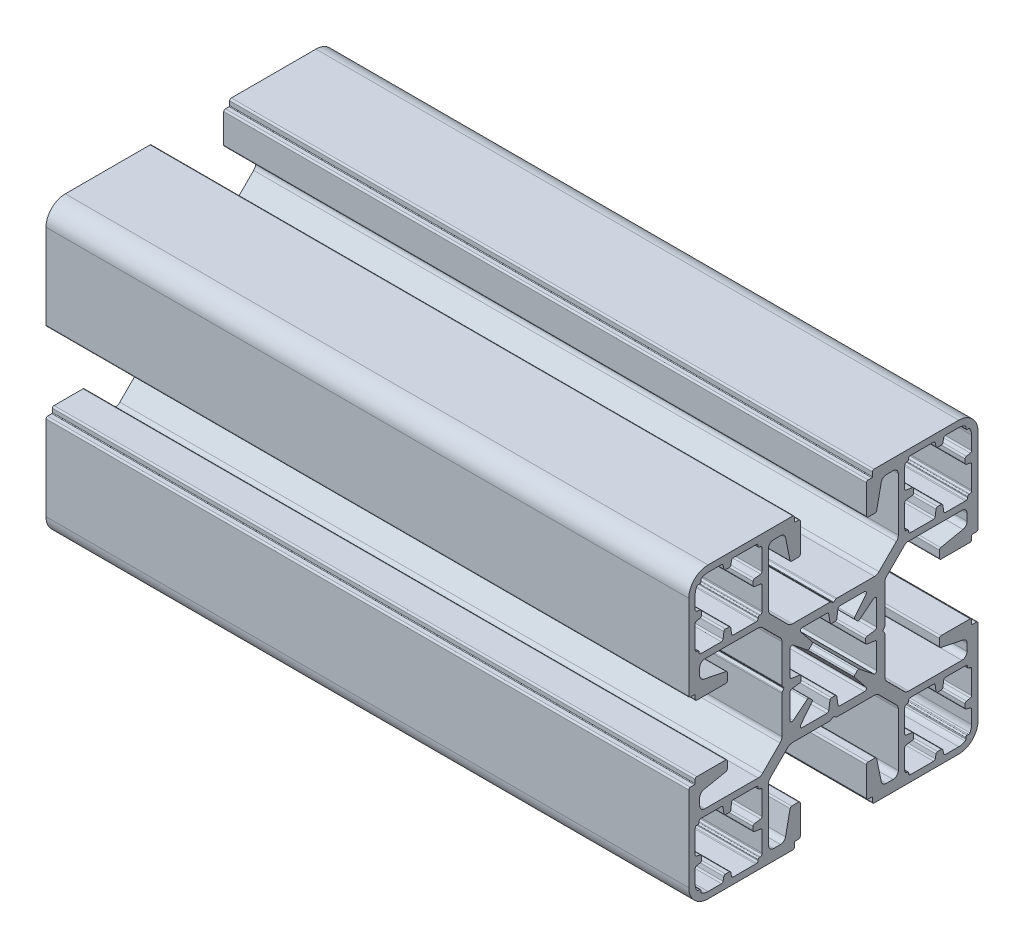
SolidWorks part; units mm, degrees
material "6063-T6"
ref_plane "Спереди" through (0, 0, 0) normal (0, 0, 1) x (1, 0, 0)
ref_plane "Сверху" through (0, 0, 0) normal (0, 1, 0) x (1, 0, 0)
ref_plane "Справа" through (0, 0, 0) normal (1, 0, 0) x (0, 0, -1)
sketch "Эскиз2" plane through (0, 0, 0) normal (1, 0, 0) x (0, 0, -1)
  point P0 (0, 0)
  line B0 (-17.405, 21.5) -> (-19.5, 21.5)
  line B1 (-20.6081, 21.0252) -> (-20.6081, 20.8081)
  line B2 (-20.8081, 20.6081) -> (-21.0252, 20.6081)
  line B3 (-21.5, 19.5) -> (-21.5, 17.405)
  line B4 (-21.299, 17.1598) -> (-20.701, 17.0402)
  line B5 (-20.5, 16.7951) -> (-20.5, 16.2049)
  line B6 (-20.701, 15.9598) -> (-21.299, 15.8402)
  line B7 (-21.5, 15.595) -> (-21.5, 12.1)
  line B8 (-21.2346, 11.699) -> (-21.101, 11.699)
  line B9 (-20.901, 11.499) -> (-20.901, 11.3654)
  line B10 (-20.5, 11.1) -> (-17.4168, 11.1)
  line B11 (-17.1693, 11.3146) -> (-17.0307, 12.2854)
  line B12 (-16.7832, 12.5) -> (-16.2168, 12.5)
  line B13 (-15.9693, 12.2854) -> (-15.8307, 11.3146)
  line B14 (-15.5832, 11.1) -> (-12.1, 11.1)
  line B15 (-11.699, 11.3654) -> (-11.699, 11.499)
  line B16 (-11.499, 11.699) -> (-11.3654, 11.699)
  line B17 (-11.1, 12.1) -> (-11.1, 15.5832)
  line B18 (-11.3146, 15.8307) -> (-12.2854, 15.9693)
  line B19 (-12.5, 16.2168) -> (-12.5, 16.7832)
  line B20 (-12.2854, 17.0307) -> (-11.3146, 17.1693)
  line B21 (-11.1, 17.4168) -> (-11.1, 20.5)
  line B22 (-11.3654, 20.901) -> (-11.499, 20.901)
  line B23 (-11.699, 21.101) -> (-11.699, 21.2346)
  line B24 (-12.1, 21.5) -> (-15.595, 21.5)
  line B25 (-15.8402, 21.299) -> (-15.9598, 20.701)
  line B26 (-16.205, 20.5) -> (-16.7951, 20.5)
  line B27 (-17.0402, 20.701) -> (-17.1598, 21.299)
  line B28 (-17.405, -21.5) -> (-19.5, -21.5)
  line B29 (-20.6081, -21.0252) -> (-20.6081, -20.8081)
  line B30 (-20.8081, -20.6081) -> (-21.0252, -20.6081)
  line B31 (-21.5, -19.5) -> (-21.5, -17.405)
  line B32 (-21.299, -17.1598) -> (-20.701, -17.0402)
  line B33 (-20.5, -16.7951) -> (-20.5, -16.2049)
  line B34 (-20.701, -15.9598) -> (-21.299, -15.8402)
  line B35 (-21.5, -15.595) -> (-21.5, -12.1)
  line B36 (-21.2346, -11.699) -> (-21.101, -11.699)
  line B37 (-20.901, -11.499) -> (-20.901, -11.3654)
  line B38 (-20.5, -11.1) -> (-17.4168, -11.1)
  line B39 (-17.1693, -11.3146) -> (-17.0307, -12.2854)
  line B40 (-16.7832, -12.5) -> (-16.2168, -12.5)
  line B41 (-15.9693, -12.2854) -> (-15.8307, -11.3146)
  line B42 (-15.5832, -11.1) -> (-12.1, -11.1)
  line B43 (-11.699, -11.3654) -> (-11.699, -11.499)
  line B44 (-11.499, -11.699) -> (-11.3654, -11.699)
  line B45 (-11.1, -12.1) -> (-11.1, -15.5832)
  line B46 (-11.3146, -15.8307) -> (-12.2854, -15.9693)
  line B47 (-12.5, -16.2168) -> (-12.5, -16.7832)
  line B48 (-12.2854, -17.0307) -> (-11.3146, -17.1693)
  line B49 (-11.1, -17.4168) -> (-11.1, -20.5)
  line B50 (-11.3654, -20.901) -> (-11.499, -20.901)
  line B51 (-11.699, -21.101) -> (-11.699, -21.2346)
  line B52 (-12.1, -21.5) -> (-15.595, -21.5)
  line B53 (-15.8402, -21.299) -> (-15.9598, -20.701)
  line B54 (-16.205, -20.5) -> (-16.7951, -20.5)
  line B55 (-17.0402, -20.701) -> (-17.1598, -21.299)
  line B56 (17.405, 21.5) -> (19.5, 21.5)
  line B57 (20.6081, 21.0252) -> (20.6081, 20.8081)
  line B58 (20.8081, 20.6081) -> (21.0252, 20.6081)
  line B59 (21.5, 19.5) -> (21.5, 17.405)
  line B60 (21.299, 17.1598) -> (20.701, 17.0402)
  line B61 (20.5, 16.795) -> (20.5, 16.2049)
  line B62 (20.701, 15.9598) -> (21.299, 15.8402)
  line B63 (21.5, 15.595) -> (21.5, 12.1)
  line B64 (21.2346, 11.699) -> (21.101, 11.699)
  line B65 (20.901, 11.499) -> (20.901, 11.3654)
  line B66 (20.5, 11.1) -> (17.4168, 11.1)
  line B67 (17.1693, 11.3146) -> (17.0307, 12.2854)
  line B68 (16.7832, 12.5) -> (16.2168, 12.5)
  line B69 (15.9693, 12.2854) -> (15.8307, 11.3146)
  line B70 (15.5832, 11.1) -> (12.1, 11.1)
  line B71 (11.699, 11.3654) -> (11.699, 11.499)
  line B72 (11.499, 11.699) -> (11.3654, 11.699)
  line B73 (11.1, 12.1) -> (11.1, 15.5832)
  line B74 (11.3146, 15.8307) -> (12.2854, 15.9693)
  line B75 (12.5, 16.2168) -> (12.5, 16.7832)
  line B76 (12.2854, 17.0307) -> (11.3146, 17.1693)
  line B77 (11.1, 17.4168) -> (11.1, 20.5)
  line B78 (11.3654, 20.901) -> (11.499, 20.901)
  line B79 (11.699, 21.101) -> (11.699, 21.2346)
  line B80 (12.1, 21.5) -> (15.595, 21.5)
  line B81 (15.8402, 21.299) -> (15.9598, 20.701)
  line B82 (16.2049, 20.5) -> (16.795, 20.5)
  line B83 (17.0402, 20.701) -> (17.1598, 21.299)
  line B84 (17.405, -21.5) -> (19.5, -21.5)
  line B85 (20.6081, -21.0252) -> (20.6081, -20.8081)
  line B86 (20.8081, -20.6081) -> (21.0252, -20.6081)
  line B87 (21.5, -19.5) -> (21.5, -17.405)
  line B88 (21.299, -17.1598) -> (20.701, -17.0402)
  line B89 (20.5, -16.795) -> (20.5, -16.2049)
  line B90 (20.701, -15.9598) -> (21.299, -15.8402)
  line B91 (21.5, -15.595) -> (21.5, -12.1)
  line B92 (21.2346, -11.699) -> (21.101, -11.699)
  line B93 (20.901, -11.499) -> (20.901, -11.3654)
  line B94 (20.5, -11.1) -> (17.4168, -11.1)
  line B95 (17.1693, -11.3146) -> (17.0307, -12.2854)
  line B96 (16.7832, -12.5) -> (16.2168, -12.5)
  line B97 (15.9693, -12.2854) -> (15.8307, -11.3146)
  line B98 (15.5832, -11.1) -> (12.1, -11.1)
  line B99 (11.699, -11.3654) -> (11.699, -11.499)
  line B100 (11.499, -11.699) -> (11.3654, -11.699)
  line B101 (11.1, -12.1) -> (11.1, -15.5832)
  line B102 (11.3146, -15.8307) -> (12.2854, -15.9693)
  line B103 (12.5, -16.2168) -> (12.5, -16.7832)
  line B104 (12.2854, -17.0307) -> (11.3146, -17.1693)
  line B105 (11.1, -17.4168) -> (11.1, -20.5)
  line B106 (11.3654, -20.901) -> (11.499, -20.901)
  line B107 (11.699, -21.101) -> (11.699, -21.2346)
  line B108 (12.1, -21.5) -> (15.595, -21.5)
  line B109 (15.8402, -21.299) -> (15.9598, -20.701)
  line B110 (16.2049, -20.5) -> (16.795, -20.5)
  line B111 (17.0402, -20.701) -> (17.1598, -21.299)
  line B112 (-6.325, -22.5) -> (-19.5, -22.5)
  line B113 (-22.5, -19.5) -> (-22.5, -6.325)
  line B114 (-22.25, -6.075) -> (-21.6, -6.075)
  line B115 (-21.5, -5.975) -> (-21.5, -5.4)
  line B116 (-21.25, -5.15) -> (-16.75, -5.15)
  line B117 (-16.5, -5.4) -> (-16.5, -6.4957)
  line B118 (-16.7001, -6.7407) -> (-20.1595, -7.4447)
  line B119 (-20.8, -8.2286) -> (-20.8, -9.3)
  line B120 (-20, -10.1) -> (-11.7163, -10.1)
  line B121 (-11.0092, -9.8071) -> (-8.2929, -7.0908)
  line B122 (-8, -6.3837) -> (-8, -0.5305)
  line B123 (-7.9531, -0.3846) -> (-7.7188, -0.0583)
  line B124 (-7.7188, 0.0583) -> (-7.9531, 0.3846)
  line B125 (-8, 0.5305) -> (-8, 6.3837)
  line B126 (-8.2929, 7.0908) -> (-11.0092, 9.8071)
  line B127 (-11.7163, 10.1) -> (-20, 10.1)
  line B128 (-20.8, 9.3) -> (-20.8, 8.2286)
  line B129 (-20.1595, 7.4447) -> (-16.7001, 6.7407)
  line B130 (-16.5, 6.4957) -> (-16.5, 5.4)
  line B131 (-16.75, 5.15) -> (-21.25, 5.15)
  line B132 (-21.5, 5.4) -> (-21.5, 5.975)
  line B133 (-21.6, 6.075) -> (-22.25, 6.075)
  line B134 (-22.5, 6.325) -> (-22.5, 19.5)
  line B135 (-19.5, 22.5) -> (-6.325, 22.5)
  line B136 (-6.075, 22.25) -> (-6.075, 21.6)
  line B137 (-5.975, 21.5) -> (-5.4, 21.5)
  line B138 (-5.15, 21.25) -> (-5.15, 16.75)
  line B139 (-5.4, 16.5) -> (-6.4957, 16.5)
  line B140 (-6.7407, 16.7001) -> (-7.4447, 20.1595)
  line B141 (-8.2286, 20.8) -> (-9.3, 20.8)
  line B142 (-10.1, 20) -> (-10.1, 11.7163)
  line B143 (-9.8071, 11.0092) -> (-7.0908, 8.2929)
  line B144 (-6.3837, 8) -> (-0.5305, 8)
  line B145 (-0.3846, 7.9531) -> (-0.0583, 7.7188)
  line B146 (0.0583, 7.7188) -> (0.3846, 7.9531)
  line B147 (0.5305, 8) -> (6.3837, 8)
  line B148 (7.0908, 8.2929) -> (9.8071, 11.0092)
  line B149 (10.1, 11.7163) -> (10.1, 20)
  line B150 (9.3, 20.8) -> (8.2286, 20.8)
  line B151 (7.4447, 20.1595) -> (6.7407, 16.7001)
  line B152 (6.4957, 16.5) -> (5.4, 16.5)
  line B153 (5.15, 16.75) -> (5.15, 21.25)
  line B154 (5.4, 21.5) -> (5.975, 21.5)
  line B155 (6.075, 21.6) -> (6.075, 22.25)
  line B156 (6.325, 22.5) -> (19.5, 22.5)
  line B157 (22.5, 19.5) -> (22.5, 6.325)
  line B158 (22.25, 6.075) -> (21.6, 6.075)
  line B159 (21.5, 5.975) -> (21.5, 5.4)
  line B160 (21.25, 5.15) -> (16.75, 5.15)
  line B161 (16.5, 5.4) -> (16.5, 6.4957)
  line B162 (16.7001, 6.7407) -> (20.1595, 7.4447)
  line B163 (20.8, 8.2286) -> (20.8, 9.3)
  line B164 (20, 10.1) -> (11.7163, 10.1)
  line B165 (11.0092, 9.8071) -> (8.2929, 7.0908)
  line B166 (8, 6.3837) -> (8, 0.5305)
  line B167 (7.9531, 0.3846) -> (7.7188, 0.0583)
  line B168 (7.7188, -0.0583) -> (7.9531, -0.3846)
  line B169 (8, -0.5305) -> (8, -6.3837)
  line B170 (8.2929, -7.0908) -> (11.0092, -9.8071)
  line B171 (11.7163, -10.1) -> (20, -10.1)
  line B172 (20.8, -9.3) -> (20.8, -8.2286)
  line B173 (20.1595, -7.4447) -> (16.7001, -6.7407)
  line B174 (16.5, -6.4957) -> (16.5, -5.4)
  line B175 (16.75, -5.15) -> (21.25, -5.15)
  line B176 (21.5, -5.4) -> (21.5, -5.975)
  line B177 (21.6, -6.075) -> (22.25, -6.075)
  line B178 (22.5, -6.325) -> (22.5, -19.5)
  line B179 (19.5, -22.5) -> (6.325, -22.5)
  line B180 (6.075, -22.25) -> (6.075, -21.6)
  line B181 (5.975, -21.5) -> (5.4, -21.5)
  line B182 (5.15, -21.25) -> (5.15, -16.75)
  line B183 (5.4, -16.5) -> (6.4957, -16.5)
  line B184 (6.7407, -16.7001) -> (7.4447, -20.1595)
  line B185 (8.2286, -20.8) -> (9.3, -20.8)
  line B186 (10.1, -20) -> (10.1, -11.7163)
  line B187 (9.8071, -11.0092) -> (7.0908, -8.2929)
  line B188 (6.3837, -8) -> (0.5305, -8)
  line B189 (0.3846, -7.9531) -> (0.0583, -7.7188)
  line B190 (-0.0583, -7.7188) -> (-0.3846, -7.9531)
  line B191 (-0.5305, -8) -> (-6.3837, -8)
  line B192 (-7.0908, -8.2929) -> (-9.8071, -11.0092)
  line B193 (-10.1, -11.7163) -> (-10.1, -20)
  line B194 (-9.3, -20.8) -> (-8.2286, -20.8)
  line B195 (-7.4447, -20.1595) -> (-6.7407, -16.7001)
  line B196 (-6.4957, -16.5) -> (-5.4, -16.5)
  line B197 (-5.15, -16.75) -> (-5.15, -21.25)
  line B198 (-5.4, -21.5) -> (-5.975, -21.5)
  line B199 (-6.075, -21.6) -> (-6.075, -22.25)
  line B200 (-4.8423, -6.74) -> (-1.01, -6.74)
  line B201 (-0.713, -6.4827) -> (-0.5308, -5.2144)
  line B202 (-0.2834, -5) -> (0.2834, -5)
  line B203 (0.5308, -5.2144) -> (0.713, -6.4827)
  line B204 (1.01, -6.74) -> (4.8423, -6.74)
  line B205 (5.0763, -6.2524) -> (3.3221, -4.0638)
  line B206 (3.3404, -3.7307) -> (3.7307, -3.3404)
  line B207 (4.0638, -3.3221) -> (6.2524, -5.0763)
  line B208 (6.74, -4.8423) -> (6.74, -1.01)
  line B209 (6.4827, -0.713) -> (5.2144, -0.5308)
  line B210 (5, -0.2834) -> (5, 0.2834)
  line B211 (5.2144, 0.5308) -> (6.4827, 0.713)
  line B212 (6.74, 1.01) -> (6.74, 4.8423)
  line B213 (6.2524, 5.0763) -> (4.0638, 3.3221)
  line B214 (3.7307, 3.3404) -> (3.3404, 3.7307)
  line B215 (3.3221, 4.0638) -> (5.0763, 6.2524)
  line B216 (4.8423, 6.74) -> (1.01, 6.74)
  line B217 (0.713, 6.4827) -> (0.5308, 5.2144)
  line B218 (0.2834, 5) -> (-0.2834, 5)
  line B219 (-0.5308, 5.2144) -> (-0.713, 6.4827)
  line B220 (-1.01, 6.74) -> (-4.8423, 6.74)
  line B221 (-5.0763, 6.2524) -> (-3.3221, 4.0638)
  line B222 (-3.3404, 3.7307) -> (-3.7307, 3.3404)
  line B223 (-4.0639, 3.3221) -> (-6.2524, 5.0763)
  line B224 (-6.74, 4.8423) -> (-6.74, 1.01)
  line B225 (-6.4827, 0.713) -> (-5.2144, 0.5308)
  line B226 (-5, 0.2834) -> (-5, -0.2834)
  line B227 (-5.2144, -0.5308) -> (-6.4827, -0.713)
  line B228 (-6.74, -1.01) -> (-6.74, -4.8423)
  line B229 (-6.2524, -5.0763) -> (-4.0639, -3.3221)
  line B230 (-3.7307, -3.3404) -> (-3.3404, -3.7307)
  line B231 (-3.3221, -4.0638) -> (-5.0763, -6.2524)
  arc B232 (-19.5, 21.5) -> (-20.4807, 21.243) centre (-19.5, 19.5) ccw
  arc B233 (-20.4807, 21.243) -> (-20.6081, 21.0252) centre (-20.3581, 21.0252) ccw
  arc B234 (-20.8081, 20.6081) -> (-20.6081, 20.8081) centre (-20.8081, 20.8081) ccw
  arc B235 (-21.0252, 20.6081) -> (-21.243, 20.4807) centre (-21.0252, 20.3581) ccw
  arc B236 (-21.243, 20.4807) -> (-21.5, 19.5) centre (-19.5, 19.5) ccw
  arc B237 (-21.5, 17.405) -> (-21.299, 17.1598) centre (-21.25, 17.405) ccw
  arc B238 (-20.5, 16.7951) -> (-20.701, 17.0402) centre (-20.75, 16.7951) ccw
  arc B239 (-20.701, 15.9598) -> (-20.5, 16.2049) centre (-20.75, 16.2049) ccw
  arc B240 (-21.299, 15.8402) -> (-21.5, 15.595) centre (-21.25, 15.595) ccw
  arc B241 (-21.5, 12.1) -> (-21.4795, 11.8986) centre (-20.5, 12.1) ccw
  arc B242 (-21.4795, 11.8986) -> (-21.2346, 11.699) centre (-21.2346, 11.949) ccw
  arc B243 (-20.901, 11.499) -> (-21.101, 11.699) centre (-21.101, 11.499) ccw
  arc B244 (-20.901, 11.3654) -> (-20.7014, 11.1205) centre (-20.651, 11.3654) ccw
  arc B245 (-20.7014, 11.1205) -> (-20.5, 11.1) centre (-20.5, 12.1) ccw
  arc B246 (-17.4168, 11.1) -> (-17.1693, 11.3146) centre (-17.4168, 11.35) ccw
  arc B247 (-16.7832, 12.5) -> (-17.0307, 12.2854) centre (-16.7832, 12.25) ccw
  arc B248 (-15.9693, 12.2854) -> (-16.2168, 12.5) centre (-16.2168, 12.25) ccw
  arc B249 (-15.8307, 11.3146) -> (-15.5832, 11.1) centre (-15.5832, 11.35) ccw
  arc B250 (-12.1, 11.1) -> (-11.8986, 11.1205) centre (-12.1, 12.1) ccw
  arc B251 (-11.8986, 11.1205) -> (-11.699, 11.3654) centre (-11.949, 11.3654) ccw
  arc B252 (-11.499, 11.699) -> (-11.699, 11.499) centre (-11.499, 11.499) ccw
  arc B253 (-11.3654, 11.699) -> (-11.1205, 11.8986) centre (-11.3654, 11.949) ccw
  arc B254 (-11.1205, 11.8986) -> (-11.1, 12.1) centre (-12.1, 12.1) ccw
  arc B255 (-11.1, 15.5832) -> (-11.3146, 15.8307) centre (-11.35, 15.5832) ccw
  arc B256 (-12.5, 16.2168) -> (-12.2854, 15.9693) centre (-12.25, 16.2168) ccw
  arc B257 (-12.2854, 17.0307) -> (-12.5, 16.7832) centre (-12.25, 16.7832) ccw
  arc B258 (-11.3146, 17.1693) -> (-11.1, 17.4168) centre (-11.35, 17.4168) ccw
  arc B259 (-11.1, 20.5) -> (-11.1205, 20.7014) centre (-12.1, 20.5) ccw
  arc B260 (-11.1205, 20.7014) -> (-11.3654, 20.901) centre (-11.3654, 20.651) ccw
  arc B261 (-11.699, 21.101) -> (-11.499, 20.901) centre (-11.499, 21.101) ccw
  arc B262 (-11.699, 21.2346) -> (-11.8986, 21.4795) centre (-11.949, 21.2346) ccw
  arc B263 (-11.8986, 21.4795) -> (-12.1, 21.5) centre (-12.1, 20.5) ccw
  arc B264 (-15.595, 21.5) -> (-15.8402, 21.299) centre (-15.595, 21.25) ccw
  arc B265 (-16.205, 20.5) -> (-15.9598, 20.701) centre (-16.205, 20.75) ccw
  arc B266 (-17.0402, 20.701) -> (-16.7951, 20.5) centre (-16.7951, 20.75) ccw
  arc B267 (-17.1598, 21.299) -> (-17.405, 21.5) centre (-17.405, 21.25) ccw
  arc B268 (-20.4807, -21.243) -> (-19.5, -21.5) centre (-19.5, -19.5) ccw
  arc B269 (-20.6081, -21.0252) -> (-20.4807, -21.243) centre (-20.3581, -21.0252) ccw
  arc B270 (-20.6081, -20.8081) -> (-20.8081, -20.6081) centre (-20.8081, -20.8081) ccw
  arc B271 (-21.243, -20.4807) -> (-21.0252, -20.6081) centre (-21.0252, -20.3581) ccw
  arc B272 (-21.5, -19.5) -> (-21.243, -20.4807) centre (-19.5, -19.5) ccw
  arc B273 (-21.299, -17.1598) -> (-21.5, -17.405) centre (-21.25, -17.405) ccw
  arc B274 (-20.701, -17.0402) -> (-20.5, -16.7951) centre (-20.75, -16.7951) ccw
  arc B275 (-20.5, -16.2049) -> (-20.701, -15.9598) centre (-20.75, -16.2049) ccw
  arc B276 (-21.5, -15.595) -> (-21.299, -15.8402) centre (-21.25, -15.595) ccw
  arc B277 (-21.4795, -11.8986) -> (-21.5, -12.1) centre (-20.5, -12.1) ccw
  arc B278 (-21.2346, -11.699) -> (-21.4795, -11.8986) centre (-21.2346, -11.949) ccw
  arc B279 (-21.101, -11.699) -> (-20.901, -11.499) centre (-21.101, -11.499) ccw
  arc B280 (-20.7014, -11.1205) -> (-20.901, -11.3654) centre (-20.651, -11.3654) ccw
  arc B281 (-20.5, -11.1) -> (-20.7014, -11.1205) centre (-20.5, -12.1) ccw
  arc B282 (-17.1693, -11.3146) -> (-17.4168, -11.1) centre (-17.4168, -11.35) ccw
  arc B283 (-17.0307, -12.2854) -> (-16.7832, -12.5) centre (-16.7832, -12.25) ccw
  arc B284 (-16.2168, -12.5) -> (-15.9693, -12.2854) centre (-16.2168, -12.25) ccw
  arc B285 (-15.5832, -11.1) -> (-15.8307, -11.3146) centre (-15.5832, -11.35) ccw
  arc B286 (-11.8986, -11.1205) -> (-12.1, -11.1) centre (-12.1, -12.1) ccw
  arc B287 (-11.699, -11.3654) -> (-11.8986, -11.1205) centre (-11.949, -11.3654) ccw
  arc B288 (-11.699, -11.499) -> (-11.499, -11.699) centre (-11.499, -11.499) ccw
  arc B289 (-11.1205, -11.8986) -> (-11.3654, -11.699) centre (-11.3654, -11.949) ccw
  arc B290 (-11.1, -12.1) -> (-11.1205, -11.8986) centre (-12.1, -12.1) ccw
  arc B291 (-11.3146, -15.8307) -> (-11.1, -15.5832) centre (-11.35, -15.5832) ccw
  arc B292 (-12.2854, -15.9693) -> (-12.5, -16.2168) centre (-12.25, -16.2168) ccw
  arc B293 (-12.5, -16.7832) -> (-12.2854, -17.0307) centre (-12.25, -16.7832) ccw
  arc B294 (-11.1, -17.4168) -> (-11.3146, -17.1693) centre (-11.35, -17.4168) ccw
  arc B295 (-11.1205, -20.7014) -> (-11.1, -20.5) centre (-12.1, -20.5) ccw
  arc B296 (-11.3654, -20.901) -> (-11.1205, -20.7014) centre (-11.3654, -20.651) ccw
  arc B297 (-11.499, -20.901) -> (-11.699, -21.101) centre (-11.499, -21.101) ccw
  arc B298 (-11.8986, -21.4795) -> (-11.699, -21.2346) centre (-11.949, -21.2346) ccw
  arc B299 (-12.1, -21.5) -> (-11.8986, -21.4795) centre (-12.1, -20.5) ccw
  arc B300 (-15.8402, -21.299) -> (-15.595, -21.5) centre (-15.595, -21.25) ccw
  arc B301 (-15.9598, -20.701) -> (-16.205, -20.5) centre (-16.205, -20.75) ccw
  arc B302 (-16.7951, -20.5) -> (-17.0402, -20.701) centre (-16.7951, -20.75) ccw
  arc B303 (-17.405, -21.5) -> (-17.1598, -21.299) centre (-17.405, -21.25) ccw
  arc B304 (20.4807, 21.243) -> (19.5, 21.5) centre (19.5, 19.5) ccw
  arc B305 (20.6081, 21.0252) -> (20.4807, 21.243) centre (20.3581, 21.0252) ccw
  arc B306 (20.6081, 20.8081) -> (20.8081, 20.6081) centre (20.8081, 20.8081) ccw
  arc B307 (21.243, 20.4807) -> (21.0252, 20.6081) centre (21.0252, 20.3581) ccw
  arc B308 (21.5, 19.5) -> (21.243, 20.4807) centre (19.5, 19.5) ccw
  arc B309 (21.299, 17.1598) -> (21.5, 17.405) centre (21.25, 17.405) ccw
  arc B310 (20.701, 17.0402) -> (20.5, 16.795) centre (20.75, 16.795) ccw
  arc B311 (20.5, 16.2049) -> (20.701, 15.9598) centre (20.75, 16.2049) ccw
  arc B312 (21.5, 15.595) -> (21.299, 15.8402) centre (21.25, 15.595) ccw
  arc B313 (21.4795, 11.8986) -> (21.5, 12.1) centre (20.5, 12.1) ccw
  arc B314 (21.2346, 11.699) -> (21.4795, 11.8986) centre (21.2346, 11.949) ccw
  arc B315 (21.101, 11.699) -> (20.901, 11.499) centre (21.101, 11.499) ccw
  arc B316 (20.7014, 11.1205) -> (20.901, 11.3654) centre (20.651, 11.3654) ccw
  arc B317 (20.5, 11.1) -> (20.7014, 11.1205) centre (20.5, 12.1) ccw
  arc B318 (17.1693, 11.3146) -> (17.4168, 11.1) centre (17.4168, 11.35) ccw
  arc B319 (17.0307, 12.2854) -> (16.7832, 12.5) centre (16.7832, 12.25) ccw
  arc B320 (16.2168, 12.5) -> (15.9693, 12.2854) centre (16.2168, 12.25) ccw
  arc B321 (15.5832, 11.1) -> (15.8307, 11.3146) centre (15.5832, 11.35) ccw
  arc B322 (11.8986, 11.1205) -> (12.1, 11.1) centre (12.1, 12.1) ccw
  arc B323 (11.699, 11.3654) -> (11.8986, 11.1205) centre (11.949, 11.3654) ccw
  arc B324 (11.699, 11.499) -> (11.499, 11.699) centre (11.499, 11.499) ccw
  arc B325 (11.1205, 11.8986) -> (11.3654, 11.699) centre (11.3654, 11.949) ccw
  arc B326 (11.1, 12.1) -> (11.1205, 11.8986) centre (12.1, 12.1) ccw
  arc B327 (11.3146, 15.8307) -> (11.1, 15.5832) centre (11.35, 15.5832) ccw
  arc B328 (12.2854, 15.9693) -> (12.5, 16.2168) centre (12.25, 16.2168) ccw
  arc B329 (12.5, 16.7832) -> (12.2854, 17.0307) centre (12.25, 16.7832) ccw
  arc B330 (11.1, 17.4168) -> (11.3146, 17.1693) centre (11.35, 17.4168) ccw
  arc B331 (11.1205, 20.7014) -> (11.1, 20.5) centre (12.1, 20.5) ccw
  arc B332 (11.3654, 20.901) -> (11.1205, 20.7014) centre (11.3654, 20.651) ccw
  arc B333 (11.499, 20.901) -> (11.699, 21.101) centre (11.499, 21.101) ccw
  arc B334 (11.8986, 21.4795) -> (11.699, 21.2346) centre (11.949, 21.2346) ccw
  arc B335 (12.1, 21.5) -> (11.8986, 21.4795) centre (12.1, 20.5) ccw
  arc B336 (15.8402, 21.299) -> (15.595, 21.5) centre (15.595, 21.25) ccw
  arc B337 (15.9598, 20.701) -> (16.2049, 20.5) centre (16.2049, 20.75) ccw
  arc B338 (16.795, 20.5) -> (17.0402, 20.701) centre (16.795, 20.75) ccw
  arc B339 (17.405, 21.5) -> (17.1598, 21.299) centre (17.405, 21.25) ccw
  arc B340 (19.5, -21.5) -> (20.4807, -21.243) centre (19.5, -19.5) ccw
  arc B341 (20.4807, -21.243) -> (20.6081, -21.0252) centre (20.3581, -21.0252) ccw
  arc B342 (20.8081, -20.6081) -> (20.6081, -20.8081) centre (20.8081, -20.8081) ccw
  arc B343 (21.0252, -20.6081) -> (21.243, -20.4807) centre (21.0252, -20.3581) ccw
  arc B344 (21.243, -20.4807) -> (21.5, -19.5) centre (19.5, -19.5) ccw
  arc B345 (21.5, -17.405) -> (21.299, -17.1598) centre (21.25, -17.405) ccw
  arc B346 (20.5, -16.795) -> (20.701, -17.0402) centre (20.75, -16.795) ccw
  arc B347 (20.701, -15.9598) -> (20.5, -16.2049) centre (20.75, -16.2049) ccw
  arc B348 (21.299, -15.8402) -> (21.5, -15.595) centre (21.25, -15.595) ccw
  arc B349 (21.5, -12.1) -> (21.4795, -11.8986) centre (20.5, -12.1) ccw
  arc B350 (21.4795, -11.8986) -> (21.2346, -11.699) centre (21.2346, -11.949) ccw
  arc B351 (20.901, -11.499) -> (21.101, -11.699) centre (21.101, -11.499) ccw
  arc B352 (20.901, -11.3654) -> (20.7014, -11.1205) centre (20.651, -11.3654) ccw
  arc B353 (20.7014, -11.1205) -> (20.5, -11.1) centre (20.5, -12.1) ccw
  arc B354 (17.4168, -11.1) -> (17.1693, -11.3146) centre (17.4168, -11.35) ccw
  arc B355 (16.7832, -12.5) -> (17.0307, -12.2854) centre (16.7832, -12.25) ccw
  arc B356 (15.9693, -12.2854) -> (16.2168, -12.5) centre (16.2168, -12.25) ccw
  arc B357 (15.8307, -11.3146) -> (15.5832, -11.1) centre (15.5832, -11.35) ccw
  arc B358 (12.1, -11.1) -> (11.8986, -11.1205) centre (12.1, -12.1) ccw
  arc B359 (11.8986, -11.1205) -> (11.699, -11.3654) centre (11.949, -11.3654) ccw
  arc B360 (11.499, -11.699) -> (11.699, -11.499) centre (11.499, -11.499) ccw
  arc B361 (11.3654, -11.699) -> (11.1205, -11.8986) centre (11.3654, -11.949) ccw
  arc B362 (11.1205, -11.8986) -> (11.1, -12.1) centre (12.1, -12.1) ccw
  arc B363 (11.1, -15.5832) -> (11.3146, -15.8307) centre (11.35, -15.5832) ccw
  arc B364 (12.5, -16.2168) -> (12.2854, -15.9693) centre (12.25, -16.2168) ccw
  arc B365 (12.2854, -17.0307) -> (12.5, -16.7832) centre (12.25, -16.7832) ccw
  arc B366 (11.3146, -17.1693) -> (11.1, -17.4168) centre (11.35, -17.4168) ccw
  arc B367 (11.1, -20.5) -> (11.1205, -20.7014) centre (12.1, -20.5) ccw
  arc B368 (11.1205, -20.7014) -> (11.3654, -20.901) centre (11.3654, -20.651) ccw
  arc B369 (11.699, -21.101) -> (11.499, -20.901) centre (11.499, -21.101) ccw
  arc B370 (11.699, -21.2346) -> (11.8986, -21.4795) centre (11.949, -21.2346) ccw
  arc B371 (11.8986, -21.4795) -> (12.1, -21.5) centre (12.1, -20.5) ccw
  arc B372 (15.595, -21.5) -> (15.8402, -21.299) centre (15.595, -21.25) ccw
  arc B373 (16.2049, -20.5) -> (15.9598, -20.701) centre (16.2049, -20.75) ccw
  arc B374 (17.0402, -20.701) -> (16.795, -20.5) centre (16.795, -20.75) ccw
  arc B375 (17.1598, -21.299) -> (17.405, -21.5) centre (17.405, -21.25) ccw
  arc B376 (-22.5, -19.5) -> (-19.5, -22.5) centre (-19.5, -19.5) ccw
  arc B377 (-22.25, -6.075) -> (-22.5, -6.325) centre (-22.25, -6.325) ccw
  arc B378 (-21.6, -6.075) -> (-21.5, -5.975) centre (-21.6, -5.975) ccw
  arc B379 (-21.25, -5.15) -> (-21.5, -5.4) centre (-21.25, -5.4) ccw
  arc B380 (-16.5, -5.4) -> (-16.75, -5.15) centre (-16.75, -5.4) ccw
  arc B381 (-16.7001, -6.7407) -> (-16.5, -6.4957) centre (-16.75, -6.4957) ccw
  arc B382 (-20.1595, -7.4447) -> (-20.8, -8.2286) centre (-20, -8.2286) ccw
  arc B383 (-20.8, -9.3) -> (-20, -10.1) centre (-20, -9.3) ccw
  arc B384 (-11.7163, -10.1) -> (-11.0092, -9.8071) centre (-11.7163, -9.1) ccw
  arc B385 (-8.2929, -7.0908) -> (-8, -6.3837) centre (-9, -6.3837) ccw
  arc B386 (-7.9531, -0.3846) -> (-8, -0.5305) centre (-7.75, -0.5305) ccw
  arc B387 (-7.7188, -0.0583) -> (-7.7188, 0.0583) centre (-7.8, 0) ccw
  arc B388 (-8, 0.5305) -> (-7.9531, 0.3846) centre (-7.75, 0.5305) ccw
  arc B389 (-8, 6.3837) -> (-8.2929, 7.0908) centre (-9, 6.3837) ccw
  arc B390 (-11.0092, 9.8071) -> (-11.7163, 10.1) centre (-11.7163, 9.1) ccw
  arc B391 (-20, 10.1) -> (-20.8, 9.3) centre (-20, 9.3) ccw
  arc B392 (-20.8, 8.2286) -> (-20.1595, 7.4447) centre (-20, 8.2286) ccw
  arc B393 (-16.5, 6.4957) -> (-16.7001, 6.7407) centre (-16.75, 6.4957) ccw
  arc B394 (-16.75, 5.15) -> (-16.5, 5.4) centre (-16.75, 5.4) ccw
  arc B395 (-21.5, 5.4) -> (-21.25, 5.15) centre (-21.25, 5.4) ccw
  arc B396 (-21.5, 5.975) -> (-21.6, 6.075) centre (-21.6, 5.975) ccw
  arc B397 (-22.5, 6.325) -> (-22.25, 6.075) centre (-22.25, 6.325) ccw
  arc B398 (-19.5, 22.5) -> (-22.5, 19.5) centre (-19.5, 19.5) ccw
  arc B399 (-6.075, 22.25) -> (-6.325, 22.5) centre (-6.325, 22.25) ccw
  arc B400 (-6.075, 21.6) -> (-5.975, 21.5) centre (-5.975, 21.6) ccw
  arc B401 (-5.15, 21.25) -> (-5.4, 21.5) centre (-5.4, 21.25) ccw
  arc B402 (-5.4, 16.5) -> (-5.15, 16.75) centre (-5.4, 16.75) ccw
  arc B403 (-6.7407, 16.7001) -> (-6.4957, 16.5) centre (-6.4957, 16.75) ccw
  arc B404 (-7.4447, 20.1595) -> (-8.2286, 20.8) centre (-8.2286, 20) ccw
  arc B405 (-9.3, 20.8) -> (-10.1, 20) centre (-9.3, 20) ccw
  arc B406 (-10.1, 11.7163) -> (-9.8071, 11.0092) centre (-9.1, 11.7163) ccw
  arc B407 (-7.0908, 8.2929) -> (-6.3837, 8) centre (-6.3837, 9) ccw
  arc B408 (-0.3846, 7.9531) -> (-0.5305, 8) centre (-0.5305, 7.75) ccw
  arc B409 (-0.0583, 7.7188) -> (0.0583, 7.7188) centre (0, 7.8) ccw
  arc B410 (0.5305, 8) -> (0.3846, 7.9531) centre (0.5305, 7.75) ccw
  arc B411 (6.3837, 8) -> (7.0908, 8.2929) centre (6.3837, 9) ccw
  arc B412 (9.8071, 11.0092) -> (10.1, 11.7163) centre (9.1, 11.7163) ccw
  arc B413 (10.1, 20) -> (9.3, 20.8) centre (9.3, 20) ccw
  arc B414 (8.2286, 20.8) -> (7.4447, 20.1595) centre (8.2286, 20) ccw
  arc B415 (6.4957, 16.5) -> (6.7407, 16.7001) centre (6.4957, 16.75) ccw
  arc B416 (5.15, 16.75) -> (5.4, 16.5) centre (5.4, 16.75) ccw
  arc B417 (5.4, 21.5) -> (5.15, 21.25) centre (5.4, 21.25) ccw
  arc B418 (5.975, 21.5) -> (6.075, 21.6) centre (5.975, 21.6) ccw
  arc B419 (6.325, 22.5) -> (6.075, 22.25) centre (6.325, 22.25) ccw
  arc B420 (22.5, 19.5) -> (19.5, 22.5) centre (19.5, 19.5) ccw
  arc B421 (22.25, 6.075) -> (22.5, 6.325) centre (22.25, 6.325) ccw
  arc B422 (21.6, 6.075) -> (21.5, 5.975) centre (21.6, 5.975) ccw
  arc B423 (21.25, 5.15) -> (21.5, 5.4) centre (21.25, 5.4) ccw
  arc B424 (16.5, 5.4) -> (16.75, 5.15) centre (16.75, 5.4) ccw
  arc B425 (16.7001, 6.7407) -> (16.5, 6.4957) centre (16.75, 6.4957) ccw
  arc B426 (20.1595, 7.4447) -> (20.8, 8.2286) centre (20, 8.2286) ccw
  arc B427 (20.8, 9.3) -> (20, 10.1) centre (20, 9.3) ccw
  arc B428 (11.7163, 10.1) -> (11.0092, 9.8071) centre (11.7163, 9.1) ccw
  arc B429 (8.2929, 7.0908) -> (8, 6.3837) centre (9, 6.3837) ccw
  arc B430 (7.9531, 0.3846) -> (8, 0.5305) centre (7.75, 0.5305) ccw
  arc B431 (7.7188, 0.0583) -> (7.7188, -0.0583) centre (7.8, 0) ccw
  arc B432 (8, -0.5305) -> (7.9531, -0.3846) centre (7.75, -0.5305) ccw
  arc B433 (8, -6.3837) -> (8.2929, -7.0908) centre (9, -6.3837) ccw
  arc B434 (11.0092, -9.8071) -> (11.7163, -10.1) centre (11.7163, -9.1) ccw
  arc B435 (20, -10.1) -> (20.8, -9.3) centre (20, -9.3) ccw
  arc B436 (20.8, -8.2286) -> (20.1595, -7.4447) centre (20, -8.2286) ccw
  arc B437 (16.5, -6.4957) -> (16.7001, -6.7407) centre (16.75, -6.4957) ccw
  arc B438 (16.75, -5.15) -> (16.5, -5.4) centre (16.75, -5.4) ccw
  arc B439 (21.5, -5.4) -> (21.25, -5.15) centre (21.25, -5.4) ccw
  arc B440 (21.5, -5.975) -> (21.6, -6.075) centre (21.6, -5.975) ccw
  arc B441 (22.5, -6.325) -> (22.25, -6.075) centre (22.25, -6.325) ccw
  arc B442 (19.5, -22.5) -> (22.5, -19.5) centre (19.5, -19.5) ccw
  arc B443 (6.075, -22.25) -> (6.325, -22.5) centre (6.325, -22.25) ccw
  arc B444 (6.075, -21.6) -> (5.975, -21.5) centre (5.975, -21.6) ccw
  arc B445 (5.15, -21.25) -> (5.4, -21.5) centre (5.4, -21.25) ccw
  arc B446 (5.4, -16.5) -> (5.15, -16.75) centre (5.4, -16.75) ccw
  arc B447 (6.7407, -16.7001) -> (6.4957, -16.5) centre (6.4957, -16.75) ccw
  arc B448 (7.4447, -20.1595) -> (8.2286, -20.8) centre (8.2286, -20) ccw
  arc B449 (9.3, -20.8) -> (10.1, -20) centre (9.3, -20) ccw
  arc B450 (10.1, -11.7163) -> (9.8071, -11.0092) centre (9.1, -11.7163) ccw
  arc B451 (7.0908, -8.2929) -> (6.3837, -8) centre (6.3837, -9) ccw
  arc B452 (0.3846, -7.9531) -> (0.5305, -8) centre (0.5305, -7.75) ccw
  arc B453 (0.0583, -7.7188) -> (-0.0583, -7.7188) centre (0, -7.8) ccw
  arc B454 (-0.5305, -8) -> (-0.3846, -7.9531) centre (-0.5305, -7.75) ccw
  arc B455 (-6.3837, -8) -> (-7.0908, -8.2929) centre (-6.3837, -9) ccw
  arc B456 (-9.8071, -11.0092) -> (-10.1, -11.7163) centre (-9.1, -11.7163) ccw
  arc B457 (-10.1, -20) -> (-9.3, -20.8) centre (-9.3, -20) ccw
  arc B458 (-8.2286, -20.8) -> (-7.4447, -20.1595) centre (-8.2286, -20) ccw
  arc B459 (-6.4957, -16.5) -> (-6.7407, -16.7001) centre (-6.4957, -16.75) ccw
  arc B460 (-5.15, -16.75) -> (-5.4, -16.5) centre (-5.4, -16.75) ccw
  arc B461 (-5.4, -21.5) -> (-5.15, -21.25) centre (-5.4, -21.25) ccw
  arc B462 (-5.975, -21.5) -> (-6.075, -21.6) centre (-5.975, -21.6) ccw
  arc B463 (-6.325, -22.5) -> (-6.075, -22.25) centre (-6.325, -22.25) ccw
  arc B464 (-1.01, -6.74) -> (-0.713, -6.4827) centre (-1.01, -6.44) ccw
  arc B465 (-0.2834, -5) -> (-0.5308, -5.2144) centre (-0.2834, -5.25) ccw
  arc B466 (0.5308, -5.2144) -> (0.2834, -5) centre (0.2834, -5.25) ccw
  arc B467 (0.713, -6.4827) -> (1.01, -6.74) centre (1.01, -6.44) ccw
  arc B468 (4.8423, -6.74) -> (5.0763, -6.2524) centre (4.8423, -6.44) ccw
  arc B469 (3.3404, -3.7307) -> (3.3221, -4.0638) centre (3.5171, -3.9075) ccw
  arc B470 (4.0638, -3.3221) -> (3.7307, -3.3404) centre (3.9075, -3.5171) ccw
  arc B471 (6.2524, -5.0763) -> (6.74, -4.8423) centre (6.44, -4.8423) ccw
  arc B472 (6.74, -1.01) -> (6.4827, -0.713) centre (6.44, -1.01) ccw
  arc B473 (5, -0.2834) -> (5.2144, -0.5308) centre (5.25, -0.2834) ccw
  arc B474 (5.2144, 0.5308) -> (5, 0.2834) centre (5.25, 0.2834) ccw
  arc B475 (6.4827, 0.713) -> (6.74, 1.01) centre (6.44, 1.01) ccw
  arc B476 (6.74, 4.8423) -> (6.2524, 5.0763) centre (6.44, 4.8423) ccw
  arc B477 (3.7307, 3.3404) -> (4.0638, 3.3221) centre (3.9075, 3.5171) ccw
  arc B478 (3.3221, 4.0638) -> (3.3404, 3.7307) centre (3.5171, 3.9075) ccw
  arc B479 (5.0763, 6.2524) -> (4.8423, 6.74) centre (4.8423, 6.44) ccw
  arc B480 (1.01, 6.74) -> (0.713, 6.4827) centre (1.01, 6.44) ccw
  arc B481 (0.2834, 5) -> (0.5308, 5.2144) centre (0.2834, 5.25) ccw
  arc B482 (-0.5308, 5.2144) -> (-0.2834, 5) centre (-0.2834, 5.25) ccw
  arc B483 (-0.713, 6.4827) -> (-1.01, 6.74) centre (-1.01, 6.44) ccw
  arc B484 (-4.8423, 6.74) -> (-5.0763, 6.2524) centre (-4.8423, 6.44) ccw
  arc B485 (-3.3404, 3.7307) -> (-3.3221, 4.0638) centre (-3.5171, 3.9075) ccw
  arc B486 (-4.0639, 3.3221) -> (-3.7307, 3.3404) centre (-3.9075, 3.5171) ccw
  arc B487 (-6.2524, 5.0763) -> (-6.74, 4.8423) centre (-6.44, 4.8423) ccw
  arc B488 (-6.74, 1.01) -> (-6.4827, 0.713) centre (-6.44, 1.01) ccw
  arc B489 (-5, 0.2834) -> (-5.2144, 0.5308) centre (-5.25, 0.2834) ccw
  arc B490 (-5.2144, -0.5308) -> (-5, -0.2834) centre (-5.25, -0.2834) ccw
  arc B491 (-6.4827, -0.713) -> (-6.74, -1.01) centre (-6.44, -1.01) ccw
  arc B492 (-6.74, -4.8423) -> (-6.2524, -5.0763) centre (-6.44, -4.8423) ccw
  arc B493 (-3.7307, -3.3404) -> (-4.0639, -3.3221) centre (-3.9075, -3.5171) ccw
  arc B494 (-3.3221, -4.0638) -> (-3.3404, -3.7307) centre (-3.5171, -3.9075) ccw
  arc B495 (-5.0763, -6.2524) -> (-4.8423, -6.74) centre (-4.8423, -6.44) ccw
sketch_block_instance "Блок1-2"
sketch_block "Блок1"
extrude "Бобышка-Вытянуть1" add sketch "Эскиз2" against normal blind 100
